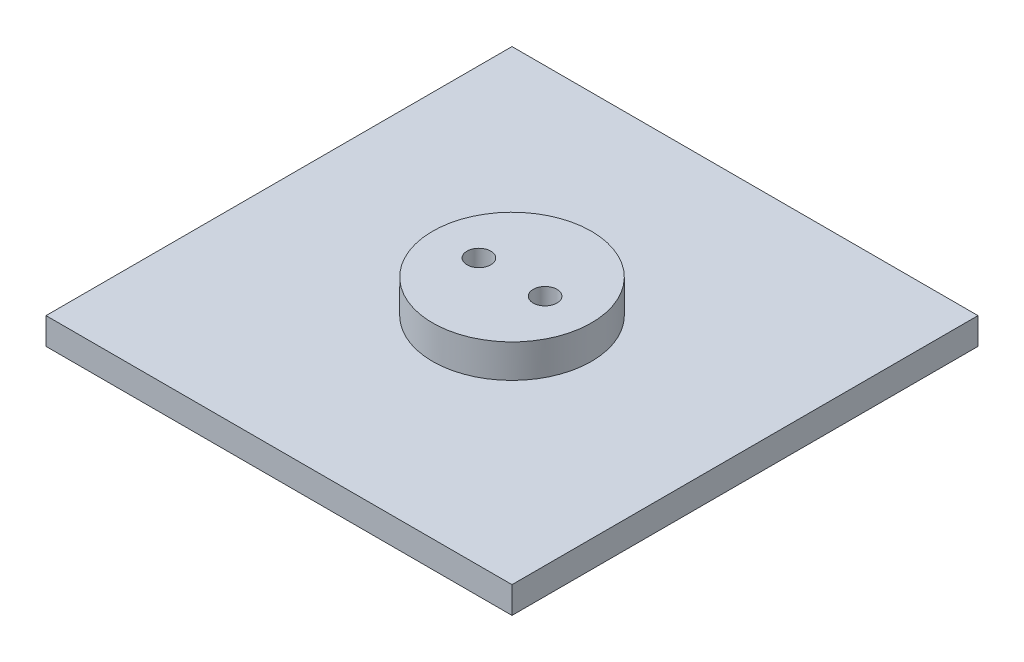
SolidWorks part; units mm, degrees
ref_plane "Front Plane" through (0, 0, 0) normal (0, 0, 1) x (1, 0, 0)
ref_plane "Top Plane" through (0, 0, 0) normal (0, 1, 0) x (1, 0, 0)
ref_plane "Right Plane" through (0, 0, 0) normal (1, 0, 0) x (0, 0, -1)
sketch "Sketch1" plane through (0, 0, 0) normal (0, 1, 0) x (1, 0, 0)
  line L1 (0, 0) -> (69.85, 0)
  line L2 (0, 0) -> (0, 69.85)
  line L3 (0, 69.85) -> (69.85, 69.85)
  line L4 (69.85, 0) -> (69.85, 69.85)
  dimension "D1" = 69.85
extrude "Boss-Extrude1" add sketch "Sketch1" along normal blind 4
sketch "Sketch2" plane through (0, 4, 0) normal (0, 1, 0) x (1, 0, 0)
  line L0 (0, 0) -> (69.85, 0) construction
  line L9 (0, 0) -> (34.925, 0) construction
  line L14 (0, 0) -> (0, 34.925) construction
  line L15 (0, 34.925) -> (34.925, 34.925) construction
  line L16 (34.925, 0) -> (34.925, 34.925) construction
  circle A0 centre (34.925, 34.925) radius 11.9062
  point P7 (34.925, 0)
  dimension "D1" = 23.8125
extrude "Boss-Extrude2" add sketch "Sketch2" along direction (0, -1, 0) on the side of the normal offset from surface (5 mm away) 9
sketch "Sketch3" plane through (0, 9, 0) normal (0, 1, 0) x (1, 0, 0)
  line L0 (0, 34.925) -> (69.85, 34.925) construction
  line L1 (0, 69.85) -> (0, 0) construction
  line L2 (69.85, 0) -> (69.85, 69.85) construction
  line L3 (31.75, 34.925) -> (38.1, 34.925) construction
  line L4 (28.1781, 34.925) -> (41.6719, 34.925) construction
  line L5 (28.1781, 34.925) -> (28.1781, 44.7351) construction
  line L6 (41.6719, 34.925) -> (41.6719, 44.7351) construction
  line L7 (28.1781, 44.7351) -> (41.6719, 44.7351) construction
  line L8 (31.75, 34.925) -> (31.75, 44.7351) construction
  line L9 (38.1, 34.925) -> (38.1, 44.7351) construction
  line L10 (31.75, 44.7351) -> (38.1, 44.7351) construction
  circle A0 centre (29.9641, 34.925) radius 1.7859
  circle A1 centre (39.8859, 34.925) radius 1.7859
  circle A3 centre (34.925, 34.925) radius 11.9062 construction
  point P10 (34.925, 44.7351)
  point P22 (34.925, 34.925)
  dimension "D1" = 6.35
  dimension "D2" = 13.4937
extrude "Cut-Extrude1" cut sketch "Sketch3" against normal up to surface (9 mm away) up to face at (34.925, 0, -34.925)
equation "\".0q\"=0"
